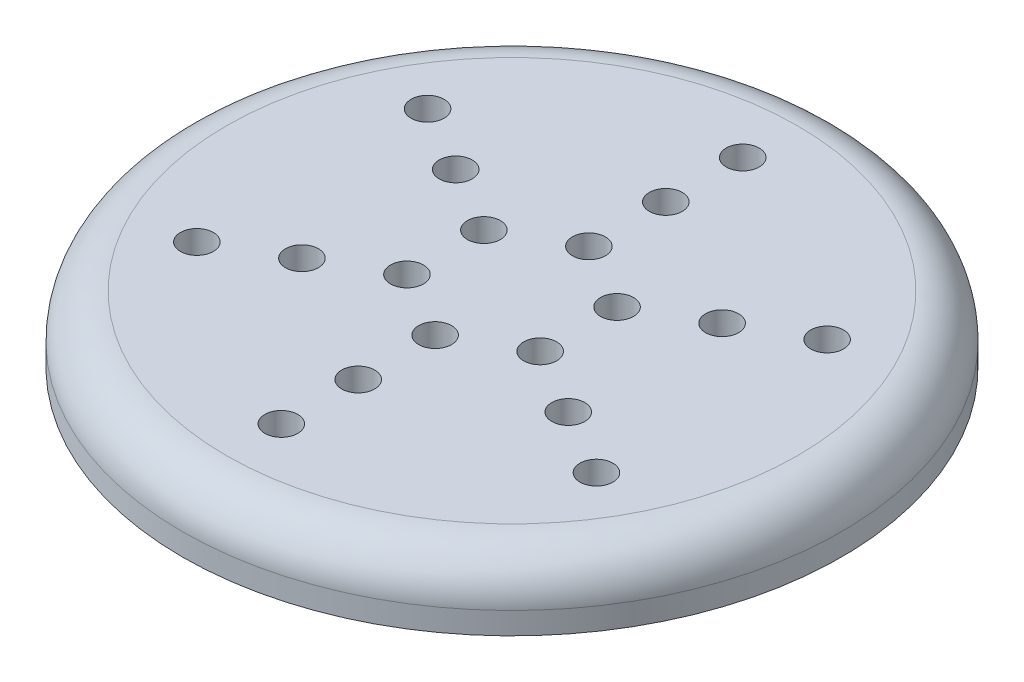
SolidWorks part; units mm, degrees
ref_plane "Front Plane" through (0, 0, 0) normal (0, 0, 1) x (1, 0, 0)
ref_plane "Top Plane" through (0, 0, 0) normal (0, 1, 0) x (1, 0, 0)
ref_plane "Right Plane" through (0, 0, 0) normal (1, 0, 0) x (0, 0, -1)
sketch "Sketch1" plane through (0, 0, 0) normal (0, 1, 0) x (1, 0, 0)
  circle A0 centre (0, 0) radius 15
  circle A1 centre (0, 10.5) radius 0.75
  circle A2 centre (0, 7) radius 0.75
  circle A3 centre (0, 3.5) radius 0.75
  circle A4 centre (3.0311, 1.75) radius 0.75
  circle A5 centre (6.0622, 3.5) radius 0.75
  circle A6 centre (9.0933, 5.25) radius 0.75
  circle A7 centre (3.0311, -1.75) radius 0.75
  circle A8 centre (6.0622, -3.5) radius 0.75
  circle A9 centre (9.0933, -5.25) radius 0.75
  circle A10 centre (0, -3.5) radius 0.75
  circle A11 centre (0, -7) radius 0.75
  circle A12 centre (0, -10.5) radius 0.75
  circle A13 centre (-3.0311, -1.75) radius 0.75
  circle A14 centre (-6.0622, -3.5) radius 0.75
  circle A15 centre (-9.0933, -5.25) radius 0.75
  circle A16 centre (-3.0311, 1.75) radius 0.75
  circle A17 centre (-6.0622, 3.5) radius 0.75
  circle A18 centre (-9.0933, 5.25) radius 0.75
  point P42 (0, 0)
  dimension "D1" = 30
  dimension "D3" = 1.5
  dimension "D4" = 1.5
  dimension "D5" = 1.5
  dimension "D2" = 3.5
  dimension "D6" = 3.5
  dimension "D7" = 3.5
  dimension "D8" = 6
extrude "Boss-Extrude1" add sketch "Sketch1" along normal blind 3
fillet "Fillet1" radius 2 1 edges at (0, 3, 15)
equation "\"D4@Sketch1\"=\"D3@Sketch1\""
equation "\"D5@Sketch1\"=\"D3@Sketch1\""
equation "\"D6@Sketch1\"=\"D2@Sketch1\""
equation "\"D7@Sketch1\"=\"D2@Sketch1\""
